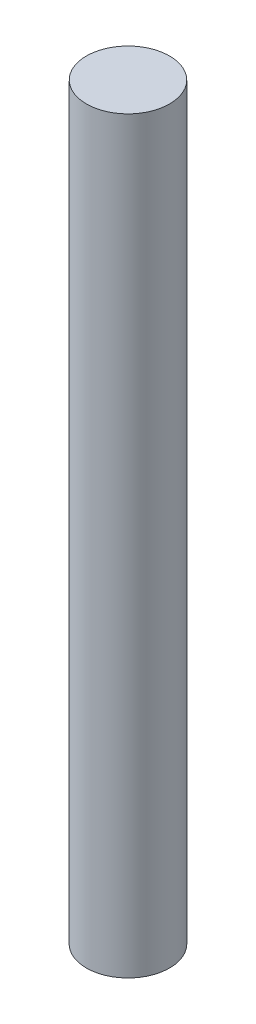
SolidWorks part; units mm, degrees
material "6063-T6"
ref_plane "Front Plane" through (0, 0, 0) normal (0, 0, 1) x (1, 0, 0)
ref_plane "Top Plane" through (0, 0, 0) normal (0, 1, 0) x (1, 0, 0)
ref_plane "Right Plane" through (0, 0, 0) normal (1, 0, 0) x (0, 0, -1)
sketch "Croquis1" plane through (0, 0, 0) normal (0, 1, 0) x (1, 0, 0)
  circle A0 centre (0, 0) radius 2.5
extrude "Saliente-Extruir1" add sketch "Croquis1" along normal blind 45
